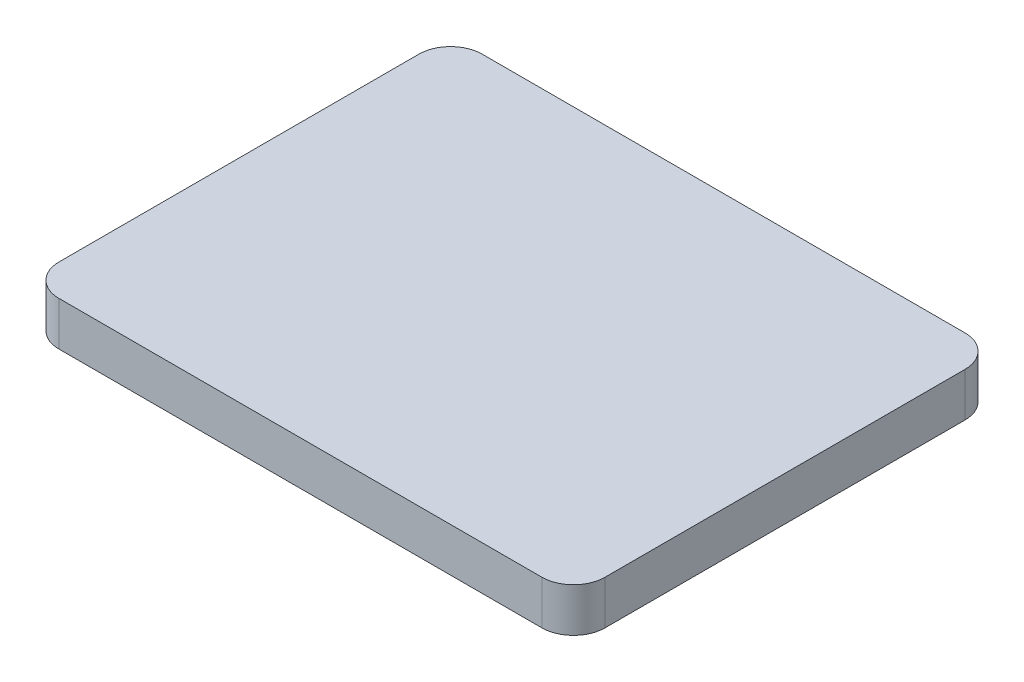
SolidWorks part; units mm, degrees
ref_plane "Front" through (0, 0, 0) normal (0, 0, 1) x (1, 0, 0)
ref_plane "Top" through (0, 0, 0) normal (0, 1, 0) x (1, 0, 0)
ref_plane "Right" through (0, 0, 0) normal (1, 0, 0) x (0, 0, -1)
sketch "草图2" plane through (0, 0, 0) normal (0, 1, 0) x (1, 0, 0)
  line L1 (-14.75, 11.25) -> (14.75, 11.25)
  line L2 (-14.75, 11.25) -> (-14.75, -11.25)
  line L3 (-14.75, -11.25) -> (14.75, -11.25)
  line L4 (14.75, 11.25) -> (14.75, -11.25)
  line L5 (-14.75, 11.25) -> (14.75, -11.25) construction
  line L6 (-14.75, -11.25) -> (14.75, 11.25) construction
  point P0 (0, 0)
  dimension "D1" = 29.5
  dimension "D2" = 22.5
extrude "layer" add sketch "草图2" along normal blind 0.5
fillet "圆角1" radius 1 4 edges at (14.75, 0.25, 11.25) (-14.75, 0.25, 11.25) (-14.75, 0.25, -11.25) (14.75, 0.25, -11.25)
sketch "草图4" plane through (0, 0.5, 0) normal (0, 1, 0) x (1, 0, 0)
  line L0 (-13.75, -12.05) -> (13.75, -12.05)
  line L1 (15.55, -10.25) -> (15.55, 10.25)
  line L2 (13.75, 12.05) -> (-13.75, 12.05)
  line L3 (-15.55, 10.25) -> (-15.55, -10.25)
  line L4 (-13.75, -11.25) -> (13.75, -11.25)
  line L5 (14.75, -10.25) -> (14.75, 10.25)
  line L6 (13.75, 11.25) -> (-13.75, 11.25)
  line L7 (-14.75, 10.25) -> (-14.75, -10.25)
  line L8 (-13.75, -11.25) -> (13.75, -11.25)
  line L9 (14.75, -10.25) -> (14.75, 10.25)
  line L10 (13.75, 11.25) -> (-13.75, 11.25)
  line L11 (-14.75, 10.25) -> (-14.75, -10.25)
  arc A0 (13.75, -12.05) -> (15.55, -10.25) centre (13.75, -10.25) ccw
  arc A1 (15.55, 10.25) -> (13.75, 12.05) centre (13.75, 10.25) ccw
  arc A2 (-13.75, 12.05) -> (-15.55, 10.25) centre (-13.75, 10.25) ccw
  arc A3 (-15.55, -10.25) -> (-13.75, -12.05) centre (-13.75, -10.25) ccw
  arc A4 (13.75, -11.25) -> (14.75, -10.25) centre (13.75, -10.25) ccw
  arc A5 (14.75, 10.25) -> (13.75, 11.25) centre (13.75, 10.25) ccw
  arc A6 (-13.75, 11.25) -> (-14.75, 10.25) centre (-13.75, 10.25) ccw
  arc A7 (-14.75, -10.25) -> (-13.75, -11.25) centre (-13.75, -10.25) ccw
  arc A8 (13.75, -11.25) -> (14.75, -10.25) centre (13.75, -10.25) ccw
  arc A9 (14.75, 10.25) -> (13.75, 11.25) centre (13.75, 10.25) ccw
  arc A10 (-13.75, 11.25) -> (-14.75, 10.25) centre (-13.75, 10.25) ccw
  arc A11 (-14.75, -10.25) -> (-13.75, -11.25) centre (-13.75, -10.25) ccw
  dimension "D1" = 0
  dimension "D2" = 0.8
extrude "凸台-拉伸1" add sketch "草图4" against normal blind 2.5
